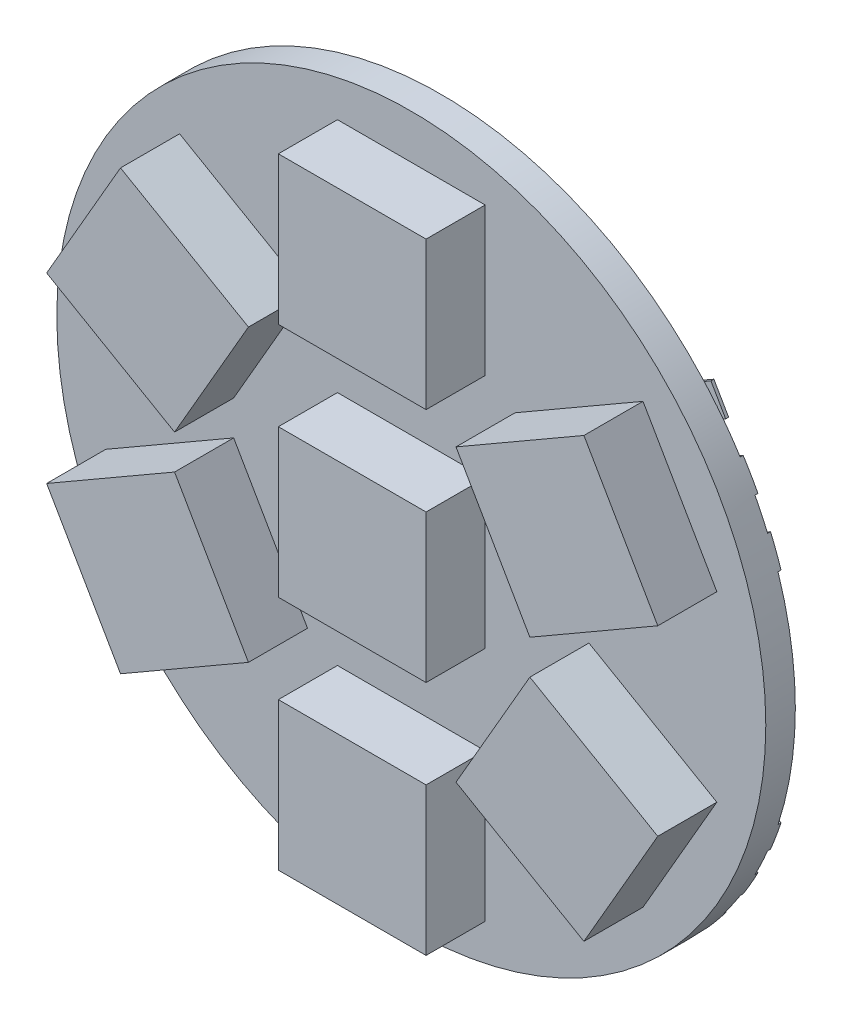
SolidWorks part; units mm, degrees
ref_plane "Alzado" through (0, 0, 0) normal (0, 0, 1) x (1, 0, 0)
ref_plane "Planta" through (0, 0, 0) normal (0, 1, 0) x (1, 0, 0)
ref_plane "Vista lateral" through (0, 0, 0) normal (1, 0, 0) x (0, 0, -1)
sketch "Croquis1" plane through (0, 0, 0) normal (0, 0, 1) x (1, 0, 0)
  circle A0 centre (0, 0) radius 12
extrude "Saliente-Extruir1" add sketch "Croquis1" along normal blind 1
sketch "Croquis2" plane through (0, 0, 1) normal (0, 0, 1) x (1, 0, 0)
  line L0 (2.5, 0) -> (-2.5, 0) construction
  line L1 (2.5, 2.5) -> (-2.5, 2.5)
  line L2 (2.5, 2.5) -> (2.5, -2.5)
  line L3 (2.5, -2.5) -> (-2.5, -2.5)
  line L4 (-2.5, 2.5) -> (-2.5, -2.5)
  line L5 (2.5, -5.5) -> (-2.5, -5.5)
  line L6 (2.5, -5.5) -> (2.5, -10.5)
  line L7 (2.5, -10.5) -> (-2.5, -10.5)
  line L8 (-2.5, -5.5) -> (-2.5, -10.5)
  line L9 (2.5, 10.5) -> (-2.5, 10.5)
  line L10 (2.5, 10.5) -> (2.5, 5.5)
  line L11 (2.5, 5.5) -> (-2.5, 5.5)
  line L12 (-2.5, 10.5) -> (-2.5, 5.5)
  line L13 (-7.8433, 7.4151) -> (-10.3433, 3.0849)
  line L14 (-7.8433, 7.4151) -> (-3.5131, 4.9151)
  line L15 (-3.5131, 4.9151) -> (-6.0131, 0.5849)
  line L16 (-10.3433, 3.0849) -> (-6.0131, 0.5849)
  line L17 (-6.0131, -0.5849) -> (-10.3433, -3.0849)
  line L18 (-6.0131, -0.5849) -> (-3.5131, -4.9151)
  line L19 (-3.5131, -4.9151) -> (-7.8433, -7.4151)
  line L20 (-10.3433, -3.0849) -> (-7.8433, -7.4151)
  line L21 (6.0131, -0.5849) -> (3.5131, -4.9151)
  line L22 (6.0131, -0.5849) -> (10.3433, -3.0849)
  line L23 (10.3433, -3.0849) -> (7.8433, -7.4151)
  line L24 (3.5131, -4.9151) -> (7.8433, -7.4151)
  line L25 (7.8433, 7.4151) -> (3.5131, 4.9151)
  line L26 (7.8433, 7.4151) -> (10.3433, 3.0849)
  line L27 (10.3433, 3.0849) -> (6.0131, 0.5849)
  line L28 (3.5131, 4.9151) -> (6.0131, 0.5849)
  line L29 (2.5, 8) -> (-2.5, 8) construction
  line L30 (2.5, -8) -> (-2.5, -8) construction
  line L31 (8.1782, -1.8349) -> (5.6782, -6.1651) construction
  line L32 (-5.6782, 6.1651) -> (-8.1782, 1.8349) construction
  line L33 (-4.7631, -2.75) -> (-9.0933, -5.25) construction
  line L34 (9.0933, 5.25) -> (4.7631, 2.75) construction
  line L35 (-6.9282, 4) -> (6.9282, -4) construction
  line L36 (-6.9282, -4) -> (6.9282, 4) construction
  circle A0 centre (0, 0) radius 8 construction
  dimension "D1" = 5
  dimension "D15" = 8
  dimension "D2" = 5
  dimension "D3" = 5
  dimension "D4" = 5
  dimension "D5" = 5
  dimension "D6" = 5
  dimension "D7" = 5
  dimension "D8" = 5
  dimension "D9" = 5
  dimension "D10" = 5
  dimension "D11" = 5
  dimension "D12" = 5
  dimension "D13" = 5
  dimension "D14" = 5
  dimension "D16" = 8
extrude "Saliente-Extruir2" add sketch "Croquis2" along normal blind 2
sketch "Croquis3" plane through (0, 0, 0) normal (0, 0, -1) x (-1, 0, 0)
  line L1 (-10.6423, 5.567) -> (-10.1423, 6.433)
  line L2 (-10.6423, 5.567) -> (-7.1782, 3.567)
  line L3 (-7.1782, 3.567) -> (-6.6782, 4.433)
  line L4 (-10.1423, 6.433) -> (-6.6782, 4.433)
  line L5 (-10.6423, 5.567) -> (-10.1423, 6.433)
  line L6 (-10.6423, 5.567) -> (-7.1782, 3.567)
  line L7 (-7.1782, 3.567) -> (-6.6782, 4.433)
  line L8 (-10.1423, 6.433) -> (-6.6782, 4.433)
  line L9 (-7.1782, -3.567) -> (-10.6423, -5.567)
  line L10 (-11.6423, 3.8349) -> (-11.1423, 4.701)
  line L11 (-8.1782, 1.8349) -> (-7.6782, 2.701)
  line L12 (-11.1423, 4.701) -> (-7.6782, 2.701)
  line L13 (-10.6423, -5.567) -> (-10.1423, -6.433)
  line L14 (-11.6423, 3.8349) -> (-8.1782, 1.8349)
  line L15 (-6.6782, -4.433) -> (-10.1423, -6.433)
  line L16 (-6.6782, -4.433) -> (-10.1423, -6.433)
  line L17 (-11.6423, -3.8349) -> (-11.1423, -4.701)
  line L18 (-9.6423, 7.299) -> (-9.1423, 8.1651)
  line L19 (-6.1782, 5.299) -> (-5.6782, 6.1651)
  line L20 (-9.1423, 8.1651) -> (-5.6782, 6.1651)
  line L21 (-9.6423, -7.299) -> (-9.1423, -8.1651)
  line L22 (-9.6423, 7.299) -> (-6.1782, 5.299)
  line L23 (-7.6782, -2.701) -> (-11.1423, -4.701)
  line L24 (-8.1782, -1.8349) -> (-11.6423, -3.8349)
  line L25 (-7.1782, -3.567) -> (-6.6782, -4.433)
  line L26 (-10.6423, -5.567) -> (-10.1423, -6.433)
  line L27 (-8.1782, -1.8349) -> (-7.6782, -2.701)
  line L28 (-5.6782, -6.1651) -> (-9.1423, -8.1651)
  line L29 (-6.1782, -5.299) -> (-9.6423, -7.299)
  line L30 (-6.1782, -5.299) -> (-5.6782, -6.1651)
  line L31 (-7.1782, -3.567) -> (-6.6782, -4.433)
  line L32 (-7.1782, -3.567) -> (-10.6423, -5.567)
  circle M34 centre (0, 0) radius 12
extrude "Saliente-Extruir3" add sketch "Croquis3" along normal blind 0.1 contours L30 L29 L28 M34 | L25 L9 L15 M34 | L27 L24 L23 M34 | L14 L11 L12 M34 | L4 L2 L3 M34 | L22 L19 L20 L18
